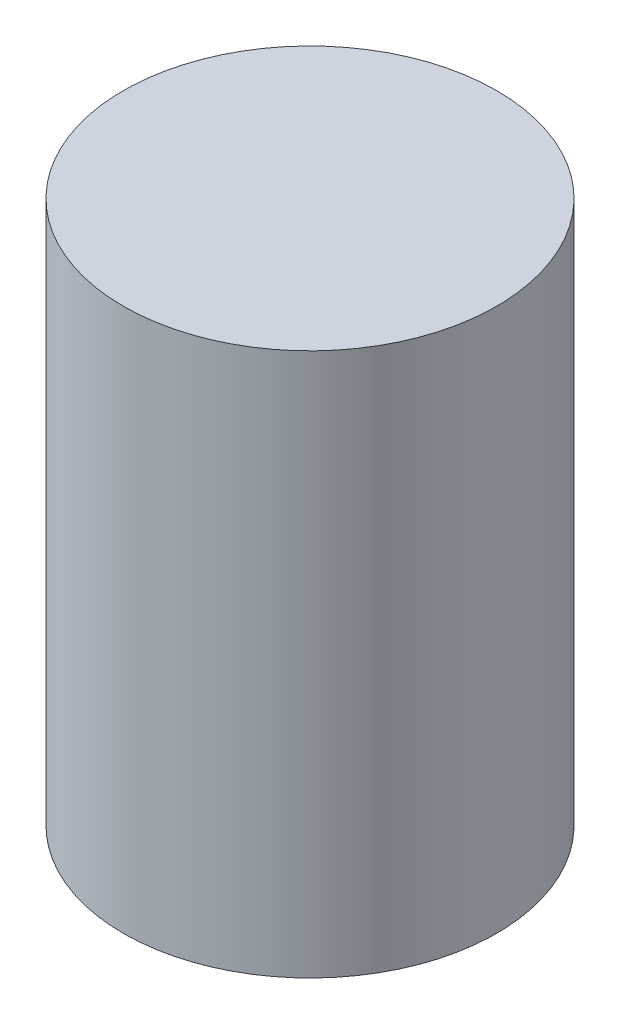
SolidWorks part; units mm, degrees
ref_plane "Front Plane" through (0, 0, 0) normal (0, 0, 1) x (1, 0, 0)
ref_plane "Top Plane" through (0, 0, 0) normal (0, 1, 0) x (1, 0, 0)
ref_plane "Right Plane" through (0, 0, 0) normal (1, 0, 0) x (0, 0, -1)
sketch "Sketch1" plane through (0, 0, 0) normal (0, 1, 0) x (1, 0, 0)
  circle A0 centre (0, 0) radius 13.75
  dimension "D1" = 27.5
extrude "Boss-Extrude1" add sketch "Sketch1" along normal blind 40
